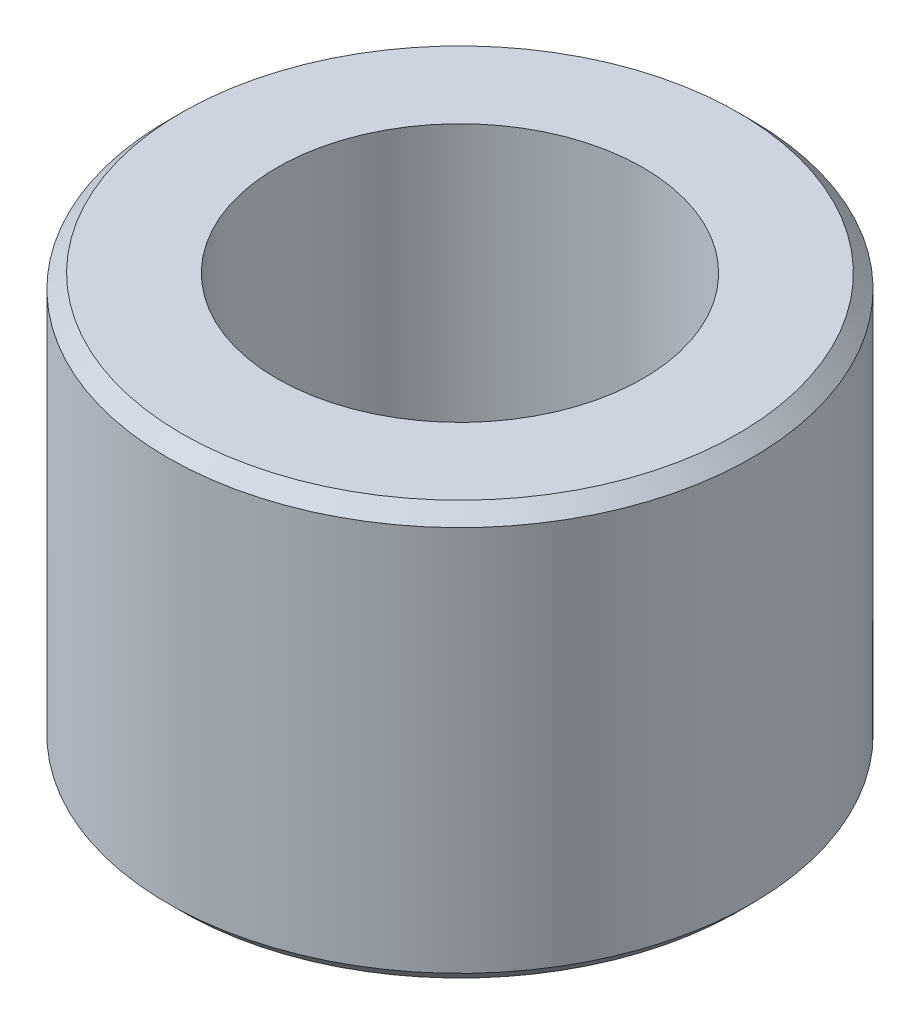
SolidWorks part; units mm, degrees
material "PVC 0.007 Plasticized"
ref_plane "Front Plane" through (0, 0, 0) normal (0, 0, 1) x (1, 0, 0)
ref_plane "Top Plane" through (0, 0, 0) normal (0, 1, 0) x (1, 0, 0)
ref_plane "Right Plane" through (0, 0, 0) normal (1, 0, 0) x (0, 0, -1)
sketch "Sketch1" plane through (0, 0, 0) normal (0, 0, 1) x (1, 0, 0)
  line L0 (10.668, 0) -> (6.6802, 0)
  line L1 (6.6802, 0) -> (6.6802, -15.113)
  line L2 (6.6802, -15.113) -> (10.668, -15.113)
  line L4 (10.668, -15.113) -> (10.668, 0)
  line L6 (0, 0) -> (0, -15.113) construction
  dimension "D1" = 6.6802
  dimension "D2" = 15.113
  dimension "D3" = 10.668
revolve "Revolve1" add sketch "Sketch1" angle 360 about L6
chamfer "Chamfer1" distance 0.508 angle 45 2 edges at (0, -15.113, -10.668) (0, 0, -10.668)
